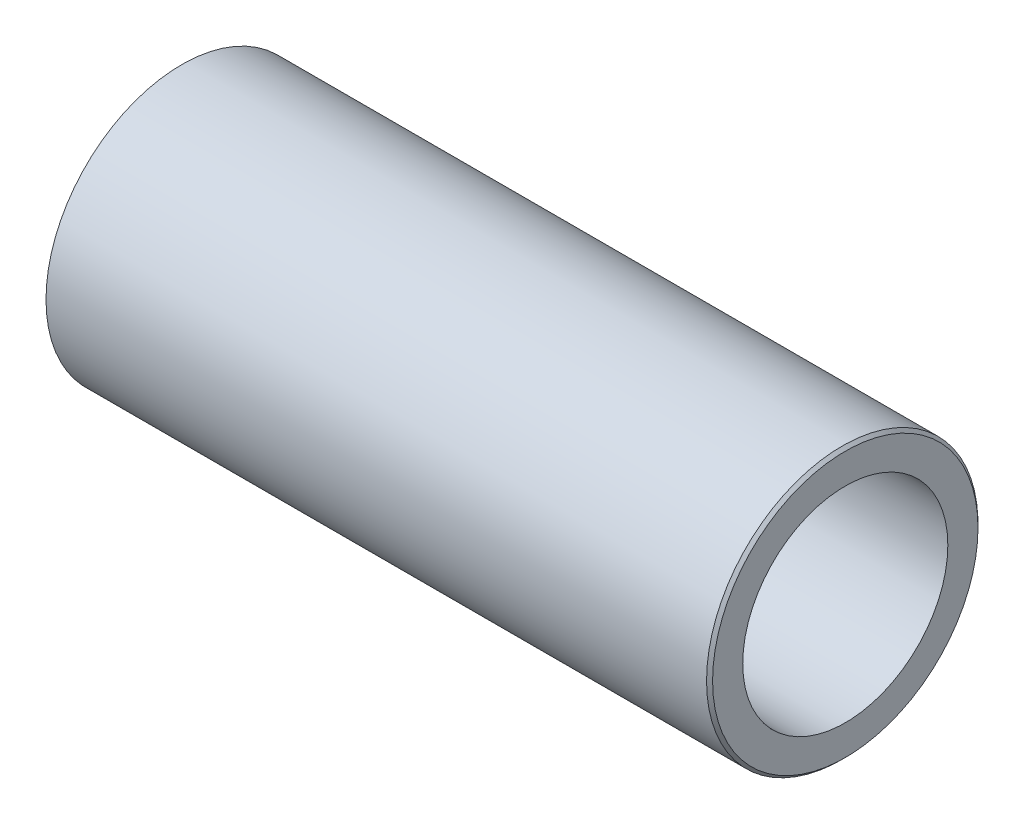
SolidWorks part; units mm, degrees
ref_plane "Front Plane" through (0, 0, 0) normal (0, 0, 1) x (1, 0, 0)
ref_plane "Top Plane" through (0, 0, 0) normal (0, 1, 0) x (1, 0, 0)
ref_plane "Right Plane" through (0, 0, 0) normal (1, 0, 0) x (0, 0, -1)
sketch "Sketch1" plane through (0, 0, 0) normal (0, 0, 1) x (1, 0, 0)
  line L0 (-55, 0) -> (55, 0) construction
  line L1 (-55, 9) -> (-51, 9)
  line L2 (-51, 9) -> (-51, 12)
  line L3 (-51, 12) -> (9, 12)
  line L4 (9, 12) -> (9, 17)
  line L5 (9, 17) -> (55, 17)
  line L6 (55, 17) -> (55, 22)
  line L7 (54.5, 22.5) -> (-55, 22.5)
  line L8 (-55, 22.5) -> (-55, 9)
  line L9 (55, 22) -> (54.5, 22.5)
  point P4 (0, 0)
  point P12 (55, 22.5)
  dimension "D1" = 110
  dimension "D2" = 4
  dimension "D3" = 60
  dimension "D4" = 46
  dimension "D5" = 18
  dimension "D6" = 24
  dimension "D7" = 34
  dimension "D8" = 45
  dimension "D9" = 0.5
  dimension "D10" = 45
revolve "Revolve1" add sketch "Sketch1" angle 360 about L0
